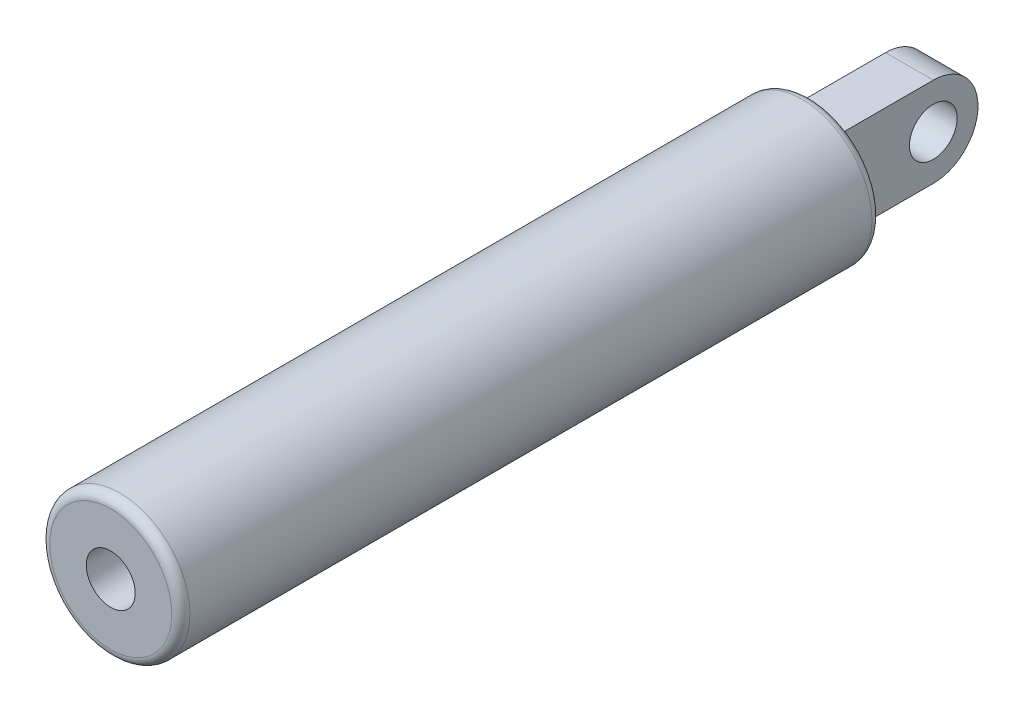
SolidWorks part; units mm, degrees
ref_plane "Front" through (0, 0, 0) normal (0, 0, 1) x (1, 0, 0)
ref_plane "Top" through (0, 0, 0) normal (0, 1, 0) x (1, 0, 0)
ref_plane "Right" through (0, 0, 0) normal (1, 0, 0) x (0, 0, -1)
sketch "Sketch1" plane through (0, 0, 0) normal (1, 0, 0) x (0, 0, -1)
  line L0 (-54.991, 0) -> (54.991, 0) construction
  line L1 (-54.991, 0) -> (-54.991, -0.254) construction
  line L2 (-25.019, 0) -> (-25.019, -0.254) construction
  line L3 (54.991, -0.254) -> (54.991, 0) construction
  line L4 (46.609, 0) -> (46.609, 5.969)
  line L5 (-13.0302, 2.0828) -> (-13.0302, 5.969)
  line L6 (-43.053, 0) -> (-43.053, 2.032) construction
  line L7 (-43.053, 2.032) -> (-13.0302, 2.032) construction
  line L8 (-13.0302, 5.969) -> (46.609, 5.969)
  line L11 (29.1846, 0) -> (46.609, 0)
  line L12 (-13.0302, 2.0828) -> (16.9926, 2.0828)
  line L13 (16.9926, 2.0828) -> (16.9926, 0) construction
  line L14 (16.9926, 2.0828) -> (29.1846, 2.0828)
  line L15 (29.1846, 2.0828) -> (29.1846, 0)
  line L16 (-13.0302, 2.0828) -> (-13.0302, 2.032) construction
  dimension "D4" = 8.382
  dimension "D5" = 11.938
  dimension "D6" = 11.9888
  dimension "E Cylinder Dia" = 11.938
  dimension "D Rod Dia" = 4.064
  dimension "D7" = 0.0508
  dimension "D8" = 12.192
  dimension "D9" = 3.8862
  dimension "D1" = 0.254
revolve "Revolve1" add sketch "Sketch1" angle 360 about L0
fillet "Fillet2" radius 0.7772 2 edges at (5.969, 0, -46.609) (5.969, 0, 13.0302)
sketch "Sketch2" plane through (0, 0, 0) normal (1, 0, 0) x (0, 0, -1)
  line L0 (46.609, 3.81) -> (54.991, 3.81)
  line L2 (46.609, -3.81) -> (46.609, 3.81)
  line L5 (46.609, 0) -> (46.609, 5.969) construction
  line L7 (46.609, -3.81) -> (54.991, -3.81)
  arc A0 (54.991, 3.81) -> (54.991, -3.81) centre (54.991, 0) cw
  circle A3 centre (54.991, 0) radius 2.032
  dimension "D4" = 4.064
  dimension "D1" = 7.62
extrude "Extrude2" add sketch "Sketch2" along normal mid plane 4.064
sketch "Sketch9" plane through (0, 0, 0) normal (1, 0, 0) x (0, 0, -1)
  line L0 (-43.053, 0) -> (-43.053, 2.032) construction
  line L2 (-43.053, 0) -> (-43.053, 2.032)
  line L3 (-43.053, 2.032) -> (-0.8382, 2.032)
  line L4 (-0.8382, 2.032) -> (-0.8382, 0)
  line L5 (-0.8382, 0) -> (-43.053, 0)
  line L6 (-43.053, 0) -> (-54.991, 0) construction
  line L8 (-0.8382, 1.016) -> (-13.0302, 1.016) construction
  line L9 (-13.0302, 1.016) -> (-13.0302, 2.032) construction
  line L10 (16.9926, 2.0828) -> (29.1846, 2.0828) construction
revolve "Revolve5" add sketch "Sketch9" angle 360 about L6
sketch "Sketch11" plane through (0, 0, 0) normal (1, 0, 0) x (0, 0, -1)
  line L0 (-43.053, 0) -> (-43.053, 3.937)
  line L1 (-43.053, 3.937) -> (-54.991, 3.937)
  line L2 (-58.928, 0) -> (-43.053, 0)
  line L3 (-58.928, 0) -> (-62.865, 0) construction
  line L4 (-54.991, 0) -> (54.991, 0) construction
  arc A0 (-54.991, 3.937) -> (-58.928, 0) centre (-54.991, 0) ccw
  circle A1 centre (-54.991, 0) radius 2.032 construction
  dimension "D2" = 4.064
  dimension "D1" = 7.874
revolve "Revolve6" add sketch "Sketch11" angle 360 about L3
sketch "Sketch12" plane through (0, 0, 0) normal (1, 0, 0) x (0, 0, -1)
  circle A0 centre (-54.991, 0) radius 2.032 construction
  circle A1 centre (-54.991, 0) radius 2.032
extrude "Cut-Extrude1" cut sketch "Sketch12" against normal through all and the other way through all
ref_plane "Plane1" through (0, 0, 54.991) normal (0, 0, 1) x (1, 0, 0)
sketch "Sketch13" plane through (0, 0, 54.991) normal (0, 0, 1) x (1, 0, 0)
  line L0 (-2.032, -3.937) -> (2.032, 3.937) construction
  line L1 (-2.032, 3.937) -> (2.032, 3.937)
  line L2 (-2.032, 3.937) -> (-2.032, -3.937)
  line L3 (-2.032, -3.937) -> (2.032, -3.937)
  line L4 (2.032, 3.937) -> (2.032, -3.937)
  dimension "D1" = 4.064
extrude "Cut-Extrude2" cut sketch "Sketch13" against normal blind 6.096 and the other way through all flip side to cut
pattern_linear "LPattern1" count 2 spacing 29.972 along (0, 0, -1) of bodies 137
sketch "Sketch10" plane through (0, 0, 0) normal (1, 0, 0) x (0, 0, -1)
  line L0 (-43.053, 2.032) -> (-13.0302, 2.032) construction
  line L2 (-43.053, -2.032) -> (-0.8382, -2.032) construction
  arc A0 (-28.3911, 2.032) -> (-28.3911, -2.032) centre (-25.019, 0) ccw
  arc A1 (-25.019, 3.937) -> (-25.019, -3.937) centre (-25.019, 0) ccw construction
delete or keep bodies "Body-Delete/Keep 1" type delete bodies bodies 139 137
equation "\"D1@Fillet2\"=\"D9@Sketch1\"/5"
equation "\"D3@LPattern1\"=\"C Stroke@Sketch1\""
